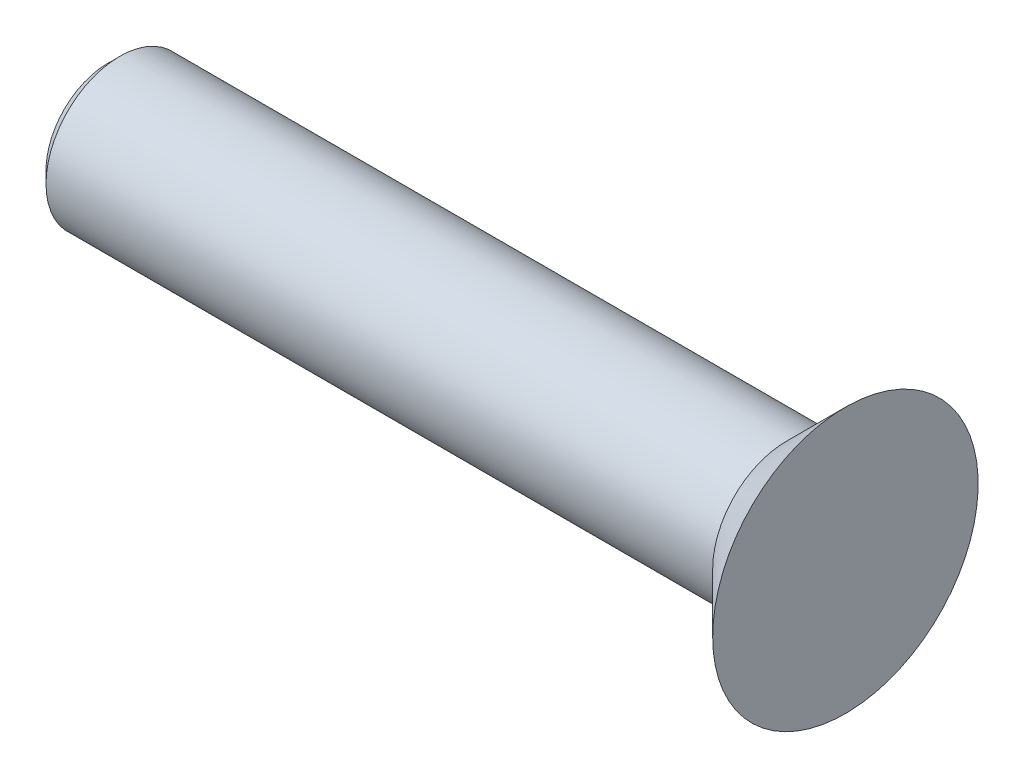
SolidWorks part; units mm, degrees
ref_plane "Plan de face" through (0, 0, 0) normal (0, 0, 1) x (1, 0, 0)
ref_plane "Plan de dessus" through (0, 0, 0) normal (0, 1, 0) x (1, 0, 0)
ref_plane "Plan de droite" through (0, 0, 0) normal (1, 0, 0) x (0, 0, -1)
sketch "Esquisse1" plane through (0, 0, 0) normal (0, 0, 1) x (1, 0, 0)
  line L0 (0, 0) -> (-25, 0)
  line L1 (-25, 0) -> (-25, 2.5)
  line L2 (-25, 2.5) -> (-2, 2.5)
  line L3 (-2, 2.5) -> (0, 4.5)
  line L4 (0, 4.5) -> (0, 0)
  line L5 (0, 0) -> (21.1509, 0) construction
  dimension "D1" = 45
  dimension "D2" = 2
  dimension "D3" = 5
  dimension "D4" = 25
revolve "Révolution1" add sketch "Esquisse1" angle 360 about L5
cosmetic thread "Représentation de filetage1" parameters "D2"=4.2
chamfer "Chanfrein1" distance 0.4 angle 45 1 edges at (-25, 0, 2.5)
